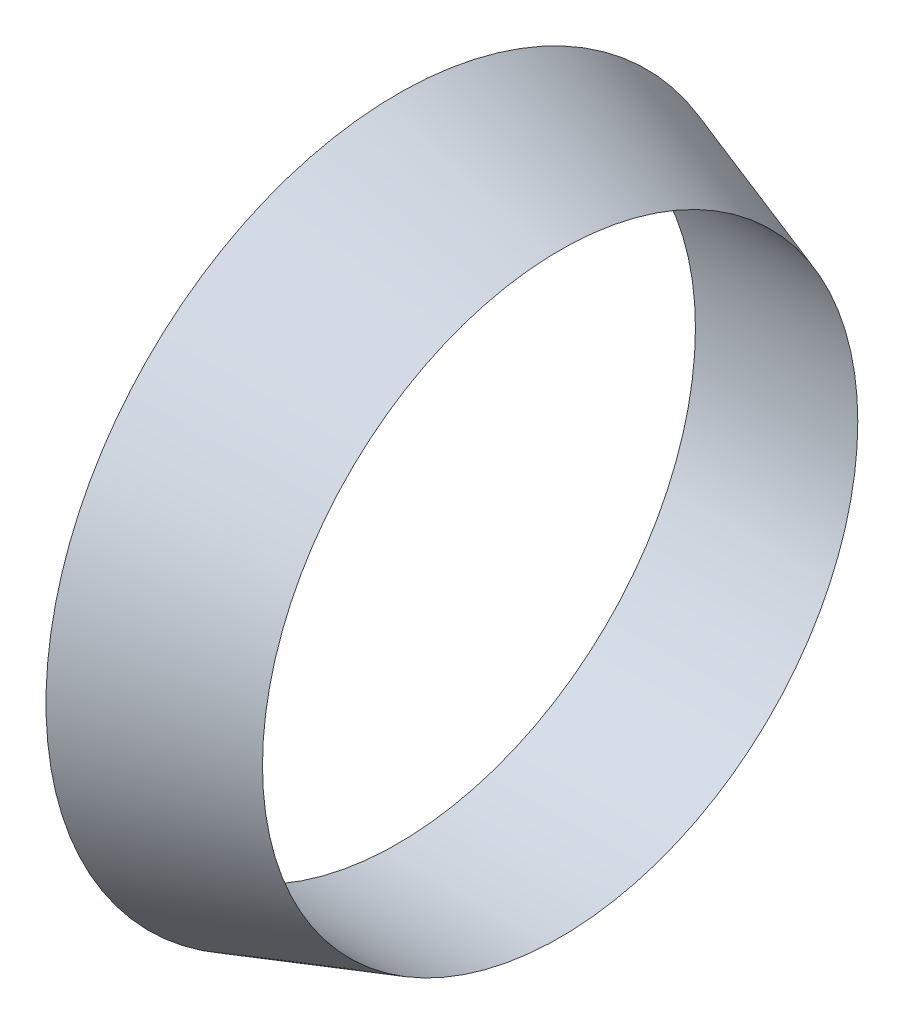
SolidWorks part; units mm, degrees
ref_plane "Front Plane" through (0, 0, 0) normal (0, 0, 1) x (1, 0, 0)
ref_plane "Top Plane" through (0, 0, 0) normal (0, 1, 0) x (1, 0, 0)
ref_plane "Right Plane" through (0, 0, 0) normal (1, 0, 0) x (0, 0, -1)
sketch "Sketch1" plane through (0, 0, 0) normal (1, 0, 0) x (0, 0, -1)
  circle A0 centre (0, 0) radius 65
  point P3 (0, 0)
  dimension "D1" = 130
ref_plane "Plane1" through (30, 0, 0) normal (1, 0, 0) x (0, 0, -1)
sketch "Sketch2" plane through (30, 0, 0) normal (1, 0, 0) x (0, 0, -1)
  circle A0 centre (0, 0) radius 55
  dimension "D1" = 110
loft "Loft1" add profiles "Sketch1", "Sketch2"
sketch "Sketch3" plane through (30, 0, 0) normal (1, 0, 0) x (0, 0, -1)
  circle A1 centre (0, 0) radius 55
  circle A2 centre (0, 0) radius 55
  dimension "D1" = 0
extrude "Cut-Extrude1" cut sketch "Sketch3" against normal through all
